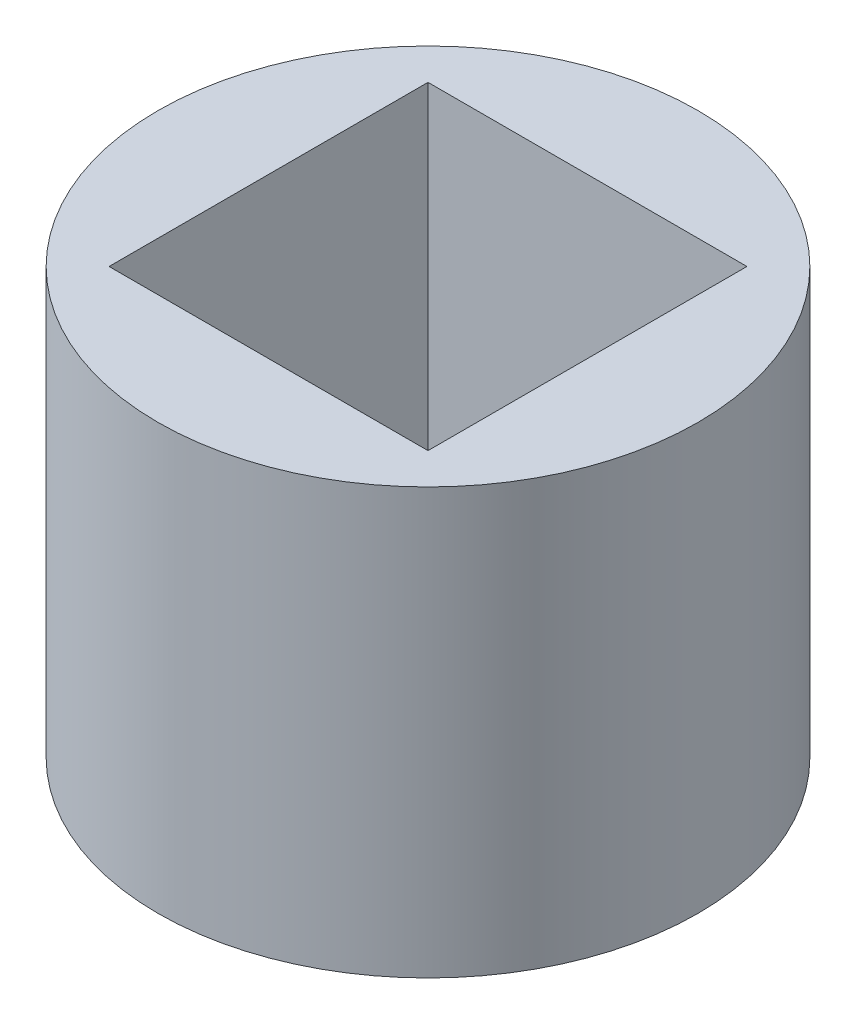
SolidWorks part; units mm, degrees
ref_plane "Front Plane" through (0, 0, 0) normal (0, 0, 1) x (1, 0, 0)
ref_plane "Top Plane" through (0, 0, 0) normal (0, 1, 0) x (1, 0, 0)
ref_plane "Right Plane" through (0, 0, 0) normal (1, 0, 0) x (0, 0, -1)
sketch "Sketch1" plane through (0, 0, 0) normal (0, 1, 0) x (1, 0, 0)
  line L1 (-7.5, -7.5) -> (7.5, -7.5)
  line L2 (-7.5, -7.5) -> (-7.5, 7.5)
  line L3 (-7.5, 7.5) -> (7.5, 7.5)
  line L4 (7.5, -7.5) -> (7.5, 7.5)
  line L5 (-7.5, -7.5) -> (7.5, 7.5) construction
  line L6 (-7.5, 7.5) -> (7.5, -7.5) construction
  circle A0 centre (0, 0) radius 12.7
  dimension "D1" = 25.4
  dimension "D2" = 15
extrude "Boss-Extrude2" add sketch "Sketch1" along normal blind 20
